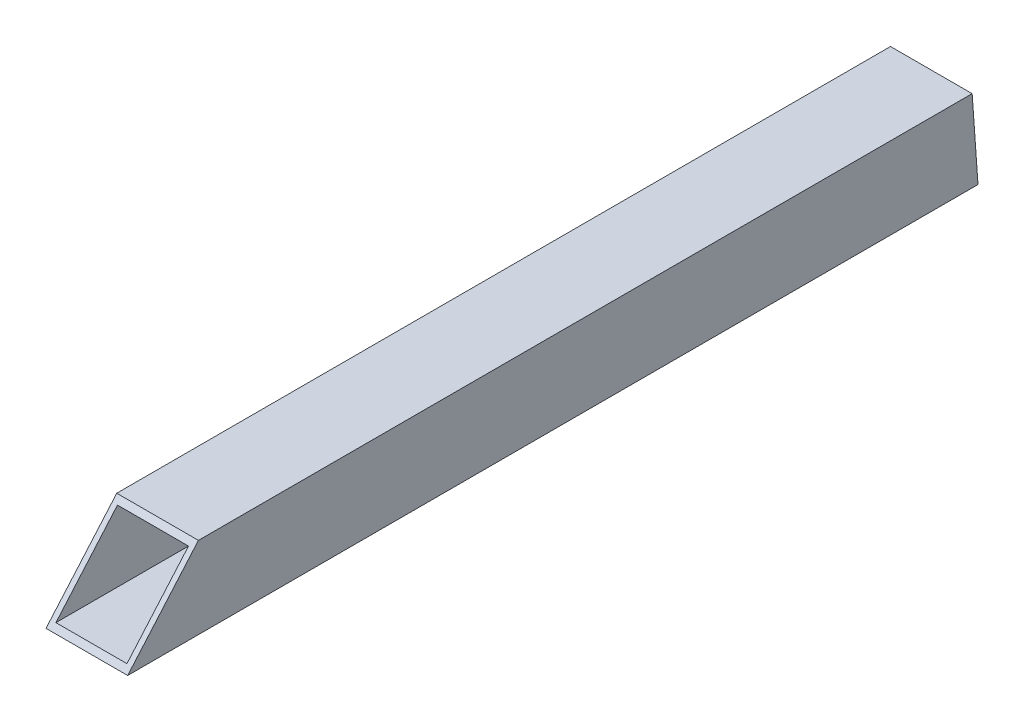
SolidWorks part; units mm, degrees
ref_plane "Front Plane" through (0, 0, 0) normal (0, 0, 1) x (1, 0, 0)
ref_plane "Top Plane" through (0, 0, 0) normal (0, 1, 0) x (1, 0, 0)
ref_plane "Right Plane" through (0, 0, 0) normal (1, 0, 0) x (0, 0, -1)
sketch "Sketch1" plane through (0, 0, 0) normal (0, 0, 1) x (1, 0, 0)
  line L1 (11.049, 11.049) -> (-11.049, 11.049)
  line L2 (11.049, 11.049) -> (11.049, -11.049)
  line L3 (11.049, -11.049) -> (-11.049, -11.049)
  line L4 (-11.049, 11.049) -> (-11.049, -11.049)
  line L5 (11.049, 11.049) -> (-11.049, -11.049) construction
  line L6 (11.049, -11.049) -> (-11.049, 11.049) construction
  line L7 (12.7, 12.7) -> (-12.7, 12.7)
  line L8 (12.7, 12.7) -> (12.7, -12.7)
  line L9 (12.7, -12.7) -> (-12.7, -12.7)
  line L10 (-12.7, 12.7) -> (-12.7, -12.7)
  line L11 (12.7, 12.7) -> (-12.7, -12.7) construction
  line L12 (12.7, -12.7) -> (-12.7, 12.7) construction
  point P0 (0, 0)
  point P6 (0, 0)
  dimension "D3" = 1.651
  dimension "D4" = 1.651
  dimension "D5" = 1.651
  dimension "D2" = 25.4
  dimension "D1" = 25.4
extrude "Boss-Extrude1" add sketch "Sketch1" along normal up to vertex (252.579 mm away)
sketch "Sketch3" plane through (0, 0, 0) normal (0, 1, 0) x (1, 0, 0)
  line L0 (0, 12.8662) -> (0, -262.1311) construction
  line L1 (0, -13.97) -> (0, 13.97) construction
ref_point "Point1"
sketch "Sketch4" plane through (0, 0, 252.579) normal (0, 0, 1) x (1, 0, 0)
  line L0 (-11.049, -11.049) -> (11.049, -11.049) construction
  line L1 (-11.049, 11.049) -> (-11.049, -11.049) construction
  line L2 (11.049, 11.049) -> (-11.049, 11.049) construction
  line L3 (11.049, -11.049) -> (11.049, 11.049) construction
  line L4 (12.7, 12.7) -> (-12.7, 12.7) construction
  line L5 (12.7, -12.7) -> (12.7, 12.7) construction
  line L6 (-12.7, -12.7) -> (12.7, -12.7) construction
  line L7 (-12.7, 12.7) -> (-12.7, -12.7) construction
  line L8 (-11.049, -11.049) -> (11.049, -11.049)
  line L9 (-11.049, 11.049) -> (-11.049, -11.049)
  line L10 (11.049, 11.049) -> (-11.049, 11.049)
  line L11 (11.049, -11.049) -> (11.049, 11.049)
  line L12 (12.7, 12.7) -> (-12.7, 12.7)
  line L13 (12.7, -12.7) -> (12.7, 12.7)
  line L14 (-12.7, -12.7) -> (12.7, -12.7)
  line L15 (-12.7, 12.7) -> (-12.7, -12.7)
extrude "Boss-Extrude2" add sketch "Sketch4" along normal blind 25.4
sketch "Sketch5" plane through (151.3216, -335.9917, -187.8078) normal (-1, 0, 0) x (0, 0.1425, -0.9898)
  line L0 (-345.8395, -431.8549) -> (-430.2231, -358.7467)
  line L1 (-430.2231, -358.7467) -> (-433.1695, -435.1008)
  line L2 (-433.1695, -435.1008) -> (-345.8395, -431.8549)
  line L3 (-345.8395, -431.8549) -> (-368.2353, -392.4517) construction
  line L4 (-125.2934, -357.4865) -> (-397.4859, -396.6616) construction
  line L5 (-345.8395, -431.8549) -> (-388.0313, -415.3008) construction
  line L8 (-388.0313, -566.2041) -> (-388.0313, -291.2069) construction
  point P2 (-349.4675, -428.7117)
  point P8 (-371.8641, -402.1282)
  point P12 (-375.222, -400.929)
  point P13 (0, 0)
  point P14 (-351.3122, -431.8278)
  point P15 (-368.2353, -412.4558)
  point P16 (-350.5009, -427.8164)
  dimension "D1" = 20
  dimension "D2" = 20
extrude "Cut-Extrude1" cut sketch "Sketch5" along normal through all
sketch "Sketch9" plane through (0, 0, 0) normal (0, 0, -1) x (-1, 0, 0)
  line L0 (-12.7, 12.7) -> (12.7, 12.7) construction
  line L1 (-11.049, 11.049) -> (11.049, 11.049) construction
  line L2 (-11.049, -11.049) -> (-11.049, 11.049) construction
  line L3 (-12.7, -12.7) -> (-12.7, 12.7) construction
  line L4 (11.049, -11.049) -> (-11.049, -11.049) construction
  line L5 (12.7, -12.7) -> (-12.7, -12.7) construction
  line L6 (11.049, 11.049) -> (11.049, -11.049) construction
  line L7 (12.7, 12.7) -> (12.7, -12.7) construction
  line L8 (-12.7, 12.7) -> (12.7, 12.7)
  line L9 (-11.049, 11.049) -> (11.049, 11.049)
  line L10 (-11.049, -11.049) -> (-11.049, 11.049)
  line L11 (-12.7, -12.7) -> (-12.7, 12.7)
  line L12 (11.049, -11.049) -> (-11.049, -11.049)
  line L13 (12.7, -12.7) -> (-12.7, -12.7)
  line L14 (11.049, 11.049) -> (11.049, -11.049)
  line L15 (12.7, 12.7) -> (12.7, -12.7)
extrude "Boss-Extrude4" add sketch "Sketch9" along normal blind 25.4
sketch "Sketch10" plane through (151.3216, -335.9917, -187.8078) normal (-1, 0, 0) x (0, 0.1425, -0.9898)
  line L0 (-135.927, -388.6707) -> (-140.1297, -329.968)
  line L1 (-103.1572, -359.3194) -> (152.5736, -359.3194) construction
  line L2 (-138.0283, -359.3194) -> (111.9717, -359.3194) construction
  line L3 (249.4717, -359.3194) -> (-25.5283, -359.3194) construction
  line L4 (-157.8243, -362.1685) -> (-140.1297, -329.968) construction
  line L5 (-125.2934, -357.4865) -> (-397.4859, -396.6616) construction
  line L6 (-118.0283, -359.3194) -> (-140.1297, -329.968) construction
  line L7 (-135.927, -388.6707) -> (-66.4046, -354.6548)
  line L8 (-66.4046, -354.6548) -> (-140.1297, -329.968)
  dimension "D1" = 20
  dimension "D2" = 20
extrude "Cut-Extrude2" cut sketch "Sketch10" along normal through all
equation "\"c1c2Len\"= 250"
equation "\"D1\"= \"c1c2Len\""
equation "\"1inchSquareTubeLen\"=25.4"
equation "\"D2@Sketch1\"=\"1inchSquareTubeLen\""
equation "\"D1@Sketch1\"=\"1inchSquareTubeLen\""
equation "\"squareTubeWallThickness\"=1.651"
equation "\"D5@Sketch1\"=\"squareTubeWallThickness\""
equation "\"D4@Sketch1\"=\"squareTubeWallThickness\""
equation "\"D3@Sketch1\"=\"squareTubeWallThickness\""
